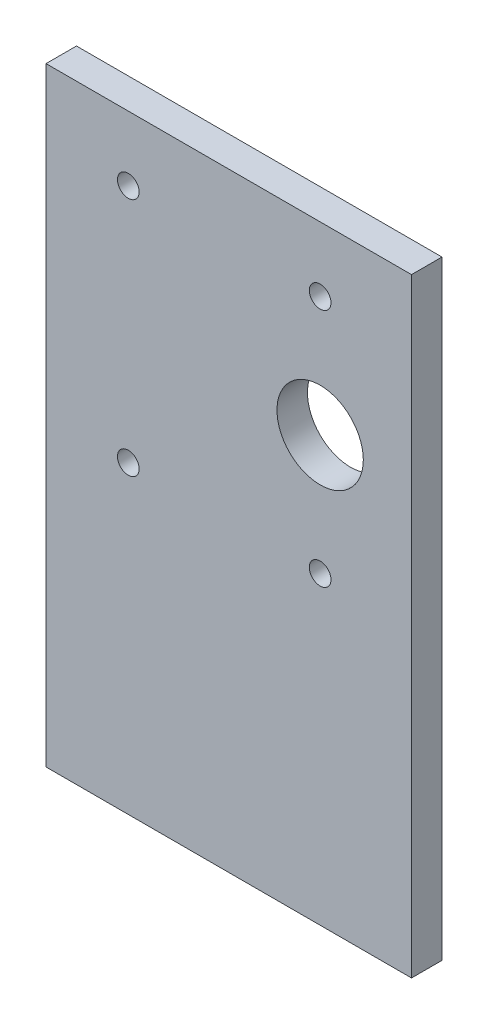
SolidWorks part; units mm, degrees
ref_plane "Front Plane" through (0, 0, 0) normal (0, 0, 1) x (1, 0, 0)
ref_plane "Top Plane" through (0, 0, 0) normal (0, 1, 0) x (1, 0, 0)
ref_plane "Right Plane" through (0, 0, 0) normal (1, 0, 0) x (0, 0, -1)
sketch "Sketch1" plane through (0, 0, 0) normal (0, 0, 1) x (1, 0, 0)
  line L1 (-17.6716, 16.0812) -> (20.4284, 16.0812)
  line L2 (-17.6716, 16.0812) -> (-17.6716, -47.4188)
  line L3 (-17.6716, -47.4188) -> (20.4284, -47.4188)
  line L4 (20.4284, 16.0812) -> (20.4284, -47.4188)
  dimension "D1" = 38.1
  dimension "D2" = 63.5
extrude "Boss-Extrude1" add sketch "Sketch1" along normal blind 3.175
sketch "Sketch2" plane through (0, 0, 3.175) normal (0, 0, 1) x (1, 0, 0)
  line L0 (20.4284, -47.4188) -> (20.4284, 16.0812) construction
  line L1 (-9.0966, 9.336) -> (10.9034, 9.336)
  line L2 (-9.0966, 9.336) -> (-9.0966, -15.664)
  line L3 (-9.0966, -15.664) -> (10.9034, -15.664)
  line L4 (10.9034, 9.336) -> (10.9034, -15.664)
  circle A0 centre (10.9034, -3.164) radius 4.5
  point P6 (10.9034, -3.164)
  point P9 (0, 0)
  dimension "D4" = 9
  dimension "D1" = 20
  dimension "D2" = 25
  dimension "D3" = 9.525
hole_wizard "#4-40 Tapped Hole1" positions "Sketch3" profile "Sketch4" tap size "#4-40" standard "ANSI Inch" end condition through all
sketch "Sketch3" plane through (0, 0, 3.175) normal (0, 0, 1) x (1, 0, 0)
  point P0 (10.9034, 9.336)
  point P3 (10.9034, -15.664)
  point P6 (-9.0966, -15.664)
  point P9 (-9.0966, 9.336)
sketch "Sketch4" plane through (10.9034, 9.336, 3.175) normal (1, 0, 0) x (0, -1, 0)
  line L0 (0, 0) -> (0, 3.175)
  line L1 (0, 3.175) -> (1.1303, 3.175)
  line L2 (1.1303, 3.175) -> (1.1303, 0)
  line L5 (1.1303, 0) -> (0, 0)
  line L11 (0, -6.35) -> (0, 107.95) construction
  dimension "Thru Tap Drill Dia." = 2.2606
  dimension "Thru Tap Drill Depth" = 3.175
cosmetic thread "Hole Thread1" parameters "D2"=2.8448
cosmetic thread "Hole Thread2" parameters "D2"=2.8448
cosmetic thread "Hole Thread3" parameters "D2"=2.8448
cosmetic thread "Hole Thread4" parameters "D2"=2.8448
extrude "Cut-Extrude1" cut sketch "Sketch2" against normal blind 3.175 contours A0
